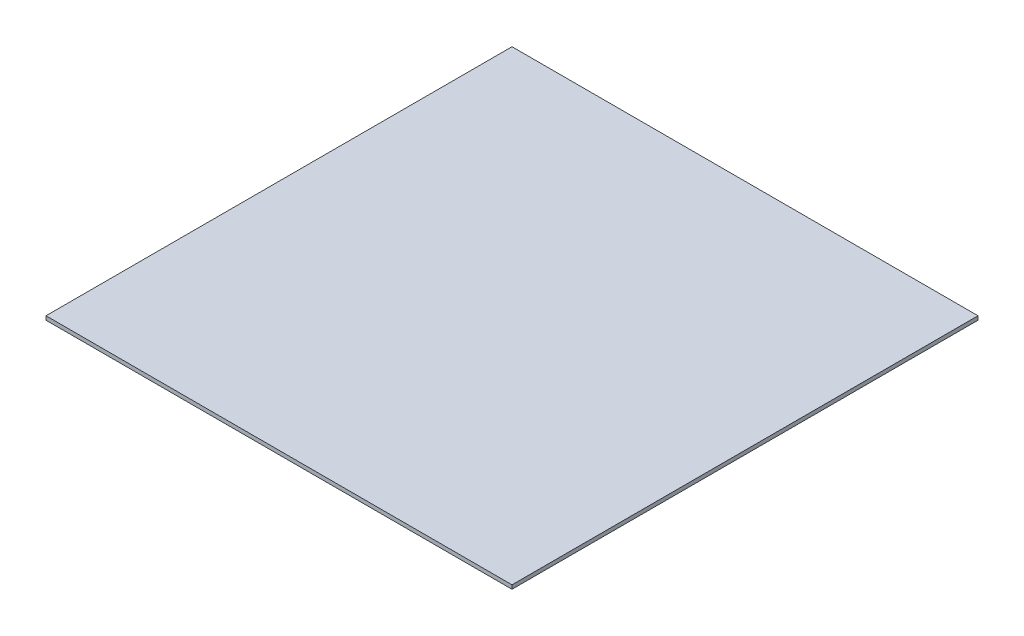
SolidWorks part; units mm, degrees
ref_plane "Front Plane" through (0, 0, 0) normal (0, 0, 1) x (1, 0, 0)
ref_plane "Top Plane" through (0, 0, 0) normal (0, 1, 0) x (1, 0, 0)
ref_plane "Right Plane" through (0, 0, 0) normal (1, 0, 0) x (0, 0, -1)
sketch "Sketch1" plane through (-19.0745, -1092.5733, -406.9173) normal (0, -1, 0) x (1, 0, 0)
  line L5 (-240, -240) -> (240, -240) construction
  line L6 (-240, -240) -> (-240, 240) construction
  line L7 (-240, 240) -> (240, 240) construction
  line L8 (240, -240) -> (240, 240) construction
  line L9 (-240, -240) -> (240, 240) construction
  line L10 (-240, 240) -> (240, -240) construction
  line L11 (300, -300) -> (-300, -300)
  line L12 (300, -300) -> (300, 300)
  line L13 (300, 300) -> (-300, 300)
  line L14 (-300, -300) -> (-300, 300)
  line L15 (300, -300) -> (-300, 300) construction
  line L16 (300, 300) -> (-300, -300) construction
  point P0 (0, 0)
  point P5 (0, 0)
  point P7 (-240, -240)
  dimension "D1" = 480
  dimension "D2" = 480
  dimension "D3" = 600
  dimension "D4" = 600
extrude "Boss-Extrude1" add sketch "Sketch1" along normal blind 5 contours L13 L14 L11 L12
sketch "Sketch3" plane through (0, -1092.5733, 0) normal (0, 1, 0) x (1, 0, 0)
  line L0 (-199.0745, 166.9173) -> (-199.0745, 226.9173)
  line L1 (-259.0745, 166.9173) -> (-199.0745, 166.9173)
  line L2 (-259.0745, 166.9173) -> (-259.0745, 226.9173)
  line L3 (-259.0745, 226.9173) -> (-199.0745, 226.9173)
  line L4 (-199.0745, 166.9173) -> (-199.0745, 226.9173)
  line L5 (-199.0745, 166.9173) -> (-139.0745, 166.9173)
  line L6 (-139.0745, 166.9173) -> (-139.0745, 226.9173)
  line L7 (-199.0745, 226.9173) -> (-139.0745, 226.9173)
  line L8 (-139.0745, 166.9173) -> (-139.0745, 226.9173)
  line L9 (-139.0745, 166.9173) -> (-79.0745, 166.9173)
  line L10 (-79.0745, 166.9173) -> (-79.0745, 226.9173)
  line L11 (-139.0745, 226.9173) -> (-79.0745, 226.9173)
  line L12 (-79.0745, 166.9173) -> (-79.0745, 226.9173)
  line L13 (-79.0745, 166.9173) -> (-19.0745, 166.9173)
  line L14 (-19.0745, 166.9173) -> (-19.0745, 226.9173)
  line L15 (-79.0745, 226.9173) -> (-19.0745, 226.9173)
  line L16 (-19.0745, 166.9173) -> (-19.0745, 226.9173)
  line L17 (-19.0745, 166.9173) -> (40.9255, 166.9173)
  line L18 (40.9255, 166.9173) -> (40.9255, 226.9173)
  line L19 (-19.0745, 226.9173) -> (40.9255, 226.9173)
  line L20 (40.9255, 166.9173) -> (40.9255, 226.9173)
  line L21 (40.9255, 166.9173) -> (100.9255, 166.9173)
  line L22 (100.9255, 166.9173) -> (100.9255, 226.9173)
  line L23 (40.9255, 226.9173) -> (100.9255, 226.9173)
  line L24 (100.9255, 166.9173) -> (100.9255, 226.9173)
  line L25 (100.9255, 166.9173) -> (160.9255, 166.9173)
  line L26 (160.9255, 166.9173) -> (160.9255, 226.9173)
  line L27 (100.9255, 226.9173) -> (160.9255, 226.9173)
  line L28 (160.9255, 166.9173) -> (160.9255, 226.9173)
  line L29 (160.9255, 166.9173) -> (220.9255, 166.9173)
  line L30 (220.9255, 166.9173) -> (220.9255, 226.9173)
  line L31 (160.9255, 226.9173) -> (220.9255, 226.9173)
  line L32 (-199.0745, 226.9173) -> (-199.0745, 286.9173)
  line L33 (-199.0745, 226.9173) -> (-139.0745, 226.9173)
  line L34 (-139.0745, 226.9173) -> (-139.0745, 286.9173)
  line L35 (-199.0745, 286.9173) -> (-139.0745, 286.9173)
  line L36 (-139.0745, 226.9173) -> (-139.0745, 286.9173)
  line L37 (-139.0745, 226.9173) -> (-79.0745, 226.9173)
  line L38 (-79.0745, 226.9173) -> (-79.0745, 286.9173)
  line L39 (-139.0745, 286.9173) -> (-79.0745, 286.9173)
  line L40 (-79.0745, 226.9173) -> (-79.0745, 286.9173)
  line L41 (-79.0745, 226.9173) -> (-19.0745, 226.9173)
  line L42 (-19.0745, 226.9173) -> (-19.0745, 286.9173)
  line L43 (-79.0745, 286.9173) -> (-19.0745, 286.9173)
  line L44 (-19.0745, 226.9173) -> (-19.0745, 286.9173)
  line L45 (-19.0745, 226.9173) -> (40.9255, 226.9173)
  line L46 (40.9255, 226.9173) -> (40.9255, 286.9173)
  line L47 (-19.0745, 286.9173) -> (40.9255, 286.9173)
  line L48 (40.9255, 226.9173) -> (40.9255, 286.9173)
  line L49 (40.9255, 226.9173) -> (100.9255, 226.9173)
  line L50 (100.9255, 226.9173) -> (100.9255, 286.9173)
  line L51 (40.9255, 286.9173) -> (100.9255, 286.9173)
  line L52 (100.9255, 226.9173) -> (100.9255, 286.9173)
  line L53 (100.9255, 226.9173) -> (160.9255, 226.9173)
  line L54 (160.9255, 226.9173) -> (160.9255, 286.9173)
  line L55 (100.9255, 286.9173) -> (160.9255, 286.9173)
  line L56 (160.9255, 226.9173) -> (160.9255, 286.9173)
  line L57 (160.9255, 226.9173) -> (220.9255, 226.9173)
  line L58 (220.9255, 226.9173) -> (220.9255, 286.9173)
  line L59 (160.9255, 286.9173) -> (220.9255, 286.9173)
  line L60 (-199.0745, 286.9173) -> (-199.0745, 346.9173)
  line L61 (-199.0745, 286.9173) -> (-139.0745, 286.9173)
  line L62 (-139.0745, 286.9173) -> (-139.0745, 346.9173)
  line L63 (-199.0745, 346.9173) -> (-139.0745, 346.9173)
  line L64 (-139.0745, 286.9173) -> (-139.0745, 346.9173)
  line L65 (-139.0745, 286.9173) -> (-79.0745, 286.9173)
  line L66 (-79.0745, 286.9173) -> (-79.0745, 346.9173)
  line L67 (-139.0745, 346.9173) -> (-79.0745, 346.9173)
  line L68 (-79.0745, 286.9173) -> (-79.0745, 346.9173)
  line L69 (-79.0745, 286.9173) -> (-19.0745, 286.9173)
  line L70 (-19.0745, 286.9173) -> (-19.0745, 346.9173)
  line L71 (-79.0745, 346.9173) -> (-19.0745, 346.9173)
  line L72 (-19.0745, 286.9173) -> (-19.0745, 346.9173)
  line L73 (-19.0745, 286.9173) -> (40.9255, 286.9173)
  line L74 (40.9255, 286.9173) -> (40.9255, 346.9173)
  line L75 (-19.0745, 346.9173) -> (40.9255, 346.9173)
  line L76 (40.9255, 286.9173) -> (40.9255, 346.9173)
  line L77 (40.9255, 286.9173) -> (100.9255, 286.9173)
  line L78 (100.9255, 286.9173) -> (100.9255, 346.9173)
  line L79 (40.9255, 346.9173) -> (100.9255, 346.9173)
  line L80 (100.9255, 286.9173) -> (100.9255, 346.9173)
  line L81 (100.9255, 286.9173) -> (160.9255, 286.9173)
  line L82 (160.9255, 286.9173) -> (160.9255, 346.9173)
  line L83 (100.9255, 346.9173) -> (160.9255, 346.9173)
  line L84 (160.9255, 286.9173) -> (160.9255, 346.9173)
  line L85 (160.9255, 286.9173) -> (220.9255, 286.9173)
  line L86 (220.9255, 286.9173) -> (220.9255, 346.9173)
  line L87 (160.9255, 346.9173) -> (220.9255, 346.9173)
  line L88 (-199.0745, 346.9173) -> (-199.0745, 406.9173)
  line L89 (-199.0745, 346.9173) -> (-139.0745, 346.9173)
  line L90 (-139.0745, 346.9173) -> (-139.0745, 406.9173)
  line L91 (-199.0745, 406.9173) -> (-139.0745, 406.9173)
  line L92 (-139.0745, 346.9173) -> (-139.0745, 406.9173)
  line L93 (-139.0745, 346.9173) -> (-79.0745, 346.9173)
  line L94 (-79.0745, 346.9173) -> (-79.0745, 406.9173)
  line L95 (-139.0745, 406.9173) -> (-79.0745, 406.9173)
  line L96 (-79.0745, 346.9173) -> (-79.0745, 406.9173)
  line L97 (-79.0745, 346.9173) -> (-19.0745, 346.9173)
  line L98 (-19.0745, 346.9173) -> (-19.0745, 406.9173)
  line L99 (-79.0745, 406.9173) -> (-19.0745, 406.9173)
  line L100 (-19.0745, 346.9173) -> (-19.0745, 406.9173)
  line L101 (-19.0745, 346.9173) -> (40.9255, 346.9173)
  line L102 (40.9255, 346.9173) -> (40.9255, 406.9173)
  line L103 (-19.0745, 406.9173) -> (40.9255, 406.9173)
  line L104 (40.9255, 346.9173) -> (40.9255, 406.9173)
  line L105 (40.9255, 346.9173) -> (100.9255, 346.9173)
  line L106 (100.9255, 346.9173) -> (100.9255, 406.9173)
  line L107 (40.9255, 406.9173) -> (100.9255, 406.9173)
  line L108 (100.9255, 346.9173) -> (100.9255, 406.9173)
  line L109 (100.9255, 346.9173) -> (160.9255, 346.9173)
  line L110 (160.9255, 346.9173) -> (160.9255, 406.9173)
  line L111 (100.9255, 406.9173) -> (160.9255, 406.9173)
  line L112 (160.9255, 346.9173) -> (160.9255, 406.9173)
  line L113 (160.9255, 346.9173) -> (220.9255, 346.9173)
  line L114 (220.9255, 346.9173) -> (220.9255, 406.9173)
  line L115 (160.9255, 406.9173) -> (220.9255, 406.9173)
  line L116 (-199.0745, 406.9173) -> (-199.0745, 466.9173)
  line L117 (-199.0745, 406.9173) -> (-139.0745, 406.9173)
  line L118 (-139.0745, 406.9173) -> (-139.0745, 466.9173)
  line L119 (-199.0745, 466.9173) -> (-139.0745, 466.9173)
  line L120 (-139.0745, 406.9173) -> (-139.0745, 466.9173)
  line L121 (-139.0745, 406.9173) -> (-79.0745, 406.9173)
  line L122 (-79.0745, 406.9173) -> (-79.0745, 466.9173)
  line L123 (-139.0745, 466.9173) -> (-79.0745, 466.9173)
  line L124 (-79.0745, 406.9173) -> (-79.0745, 466.9173)
  line L125 (-79.0745, 406.9173) -> (-19.0745, 406.9173)
  line L126 (-19.0745, 406.9173) -> (-19.0745, 466.9173)
  line L127 (-79.0745, 466.9173) -> (-19.0745, 466.9173)
  line L128 (-19.0745, 406.9173) -> (-19.0745, 466.9173)
  line L129 (-19.0745, 406.9173) -> (40.9255, 406.9173)
  line L130 (40.9255, 406.9173) -> (40.9255, 466.9173)
  line L131 (-19.0745, 466.9173) -> (40.9255, 466.9173)
  line L132 (40.9255, 406.9173) -> (40.9255, 466.9173)
  line L133 (40.9255, 406.9173) -> (100.9255, 406.9173)
  line L134 (100.9255, 406.9173) -> (100.9255, 466.9173)
  line L135 (40.9255, 466.9173) -> (100.9255, 466.9173)
  line L136 (100.9255, 406.9173) -> (100.9255, 466.9173)
  line L137 (100.9255, 406.9173) -> (160.9255, 406.9173)
  line L138 (160.9255, 406.9173) -> (160.9255, 466.9173)
  line L139 (100.9255, 466.9173) -> (160.9255, 466.9173)
  line L140 (160.9255, 406.9173) -> (160.9255, 466.9173)
  line L141 (160.9255, 406.9173) -> (220.9255, 406.9173)
  line L142 (220.9255, 406.9173) -> (220.9255, 466.9173)
  line L143 (160.9255, 466.9173) -> (220.9255, 466.9173)
  line L144 (-199.0745, 466.9173) -> (-199.0745, 526.9173)
  line L145 (-199.0745, 466.9173) -> (-139.0745, 466.9173)
  line L146 (-139.0745, 466.9173) -> (-139.0745, 526.9173)
  line L147 (-199.0745, 526.9173) -> (-139.0745, 526.9173)
  line L148 (-139.0745, 466.9173) -> (-139.0745, 526.9173)
  line L149 (-139.0745, 466.9173) -> (-79.0745, 466.9173)
  line L150 (-79.0745, 466.9173) -> (-79.0745, 526.9173)
  line L151 (-139.0745, 526.9173) -> (-79.0745, 526.9173)
  line L152 (-79.0745, 466.9173) -> (-79.0745, 526.9173)
  line L153 (-79.0745, 466.9173) -> (-19.0745, 466.9173)
  line L154 (-19.0745, 466.9173) -> (-19.0745, 526.9173)
  line L155 (-79.0745, 526.9173) -> (-19.0745, 526.9173)
  line L156 (-19.0745, 466.9173) -> (-19.0745, 526.9173)
  line L157 (-19.0745, 466.9173) -> (40.9255, 466.9173)
  line L158 (40.9255, 466.9173) -> (40.9255, 526.9173)
  line L159 (-19.0745, 526.9173) -> (40.9255, 526.9173)
  line L160 (40.9255, 466.9173) -> (40.9255, 526.9173)
  line L161 (40.9255, 466.9173) -> (100.9255, 466.9173)
  line L162 (100.9255, 466.9173) -> (100.9255, 526.9173)
  line L163 (40.9255, 526.9173) -> (100.9255, 526.9173)
  line L164 (100.9255, 466.9173) -> (100.9255, 526.9173)
  line L165 (100.9255, 466.9173) -> (160.9255, 466.9173)
  line L166 (160.9255, 466.9173) -> (160.9255, 526.9173)
  line L167 (100.9255, 526.9173) -> (160.9255, 526.9173)
  line L168 (160.9255, 466.9173) -> (160.9255, 526.9173)
  line L169 (160.9255, 466.9173) -> (220.9255, 466.9173)
  line L170 (220.9255, 466.9173) -> (220.9255, 526.9173)
  line L171 (160.9255, 526.9173) -> (220.9255, 526.9173)
  line L172 (-199.0745, 526.9173) -> (-199.0745, 586.9173)
  line L173 (-199.0745, 526.9173) -> (-139.0745, 526.9173)
  line L174 (-139.0745, 526.9173) -> (-139.0745, 586.9173)
  line L175 (-199.0745, 586.9173) -> (-139.0745, 586.9173)
  line L176 (-139.0745, 526.9173) -> (-139.0745, 586.9173)
  line L177 (-139.0745, 526.9173) -> (-79.0745, 526.9173)
  line L178 (-79.0745, 526.9173) -> (-79.0745, 586.9173)
  line L179 (-139.0745, 586.9173) -> (-79.0745, 586.9173)
  line L180 (-79.0745, 526.9173) -> (-79.0745, 586.9173)
  line L181 (-79.0745, 526.9173) -> (-19.0745, 526.9173)
  line L182 (-19.0745, 526.9173) -> (-19.0745, 586.9173)
  line L183 (-79.0745, 586.9173) -> (-19.0745, 586.9173)
  line L184 (-19.0745, 526.9173) -> (-19.0745, 586.9173)
  line L185 (-19.0745, 526.9173) -> (40.9255, 526.9173)
  line L186 (40.9255, 526.9173) -> (40.9255, 586.9173)
  line L187 (-19.0745, 586.9173) -> (40.9255, 586.9173)
  line L188 (40.9255, 526.9173) -> (40.9255, 586.9173)
  line L189 (40.9255, 526.9173) -> (100.9255, 526.9173)
  line L190 (100.9255, 526.9173) -> (100.9255, 586.9173)
  line L191 (40.9255, 586.9173) -> (100.9255, 586.9173)
  line L192 (100.9255, 526.9173) -> (100.9255, 586.9173)
  line L193 (100.9255, 526.9173) -> (160.9255, 526.9173)
  line L194 (160.9255, 526.9173) -> (160.9255, 586.9173)
  line L195 (100.9255, 586.9173) -> (160.9255, 586.9173)
  line L196 (160.9255, 526.9173) -> (160.9255, 586.9173)
  line L197 (160.9255, 526.9173) -> (220.9255, 526.9173)
  line L198 (220.9255, 526.9173) -> (220.9255, 586.9173)
  line L199 (160.9255, 586.9173) -> (220.9255, 586.9173)
  line L200 (-199.0745, 586.9173) -> (-199.0745, 646.9173)
  line L201 (-199.0745, 586.9173) -> (-139.0745, 586.9173)
  line L202 (-139.0745, 586.9173) -> (-139.0745, 646.9173)
  line L203 (-199.0745, 646.9173) -> (-139.0745, 646.9173)
  line L204 (-139.0745, 586.9173) -> (-139.0745, 646.9173)
  line L205 (-139.0745, 586.9173) -> (-79.0745, 586.9173)
  line L206 (-79.0745, 586.9173) -> (-79.0745, 646.9173)
  line L207 (-139.0745, 646.9173) -> (-79.0745, 646.9173)
  line L208 (-79.0745, 586.9173) -> (-79.0745, 646.9173)
  line L209 (-79.0745, 586.9173) -> (-19.0745, 586.9173)
  line L210 (-19.0745, 586.9173) -> (-19.0745, 646.9173)
  line L211 (-79.0745, 646.9173) -> (-19.0745, 646.9173)
  line L212 (-19.0745, 586.9173) -> (-19.0745, 646.9173)
  line L213 (-19.0745, 586.9173) -> (40.9255, 586.9173)
  line L214 (40.9255, 586.9173) -> (40.9255, 646.9173)
  line L215 (-19.0745, 646.9173) -> (40.9255, 646.9173)
  line L216 (40.9255, 586.9173) -> (40.9255, 646.9173)
  line L217 (40.9255, 586.9173) -> (100.9255, 586.9173)
  line L218 (100.9255, 586.9173) -> (100.9255, 646.9173)
  line L219 (40.9255, 646.9173) -> (100.9255, 646.9173)
  line L220 (100.9255, 586.9173) -> (100.9255, 646.9173)
  line L221 (100.9255, 586.9173) -> (160.9255, 586.9173)
  line L222 (160.9255, 586.9173) -> (160.9255, 646.9173)
  line L223 (100.9255, 646.9173) -> (160.9255, 646.9173)
  line L224 (160.9255, 586.9173) -> (160.9255, 646.9173)
  line L225 (160.9255, 586.9173) -> (220.9255, 586.9173)
  line L226 (220.9255, 586.9173) -> (220.9255, 646.9173)
  line L227 (160.9255, 646.9173) -> (220.9255, 646.9173)
  line L228 (-259.0745, 226.9173) -> (-259.0745, 286.9173)
  line L229 (-259.0745, 226.9173) -> (-199.0745, 226.9173)
  line L230 (-199.0745, 226.9173) -> (-199.0745, 286.9173)
  line L231 (-259.0745, 286.9173) -> (-199.0745, 286.9173)
  line L232 (-259.0745, 286.9173) -> (-259.0745, 346.9173)
  line L233 (-259.0745, 286.9173) -> (-199.0745, 286.9173)
  line L234 (-199.0745, 286.9173) -> (-199.0745, 346.9173)
  line L235 (-259.0745, 346.9173) -> (-199.0745, 346.9173)
  line L236 (-259.0745, 346.9173) -> (-259.0745, 406.9173)
  line L237 (-259.0745, 346.9173) -> (-199.0745, 346.9173)
  line L238 (-199.0745, 346.9173) -> (-199.0745, 406.9173)
  line L239 (-259.0745, 406.9173) -> (-199.0745, 406.9173)
  line L240 (-259.0745, 406.9173) -> (-259.0745, 466.9173)
  line L241 (-259.0745, 406.9173) -> (-199.0745, 406.9173)
  line L242 (-199.0745, 406.9173) -> (-199.0745, 466.9173)
  line L243 (-259.0745, 466.9173) -> (-199.0745, 466.9173)
  line L244 (-259.0745, 466.9173) -> (-259.0745, 526.9173)
  line L245 (-259.0745, 466.9173) -> (-199.0745, 466.9173)
  line L246 (-199.0745, 466.9173) -> (-199.0745, 526.9173)
  line L247 (-259.0745, 526.9173) -> (-199.0745, 526.9173)
  line L248 (-259.0745, 526.9173) -> (-259.0745, 586.9173)
  line L249 (-259.0745, 526.9173) -> (-199.0745, 526.9173)
  line L250 (-199.0745, 526.9173) -> (-199.0745, 586.9173)
  line L251 (-259.0745, 586.9173) -> (-199.0745, 586.9173)
  line L252 (-259.0745, 586.9173) -> (-259.0745, 646.9173)
  line L253 (-259.0745, 586.9173) -> (-199.0745, 586.9173)
  line L254 (-199.0745, 586.9173) -> (-199.0745, 646.9173)
  line L255 (-259.0745, 646.9173) -> (-199.0745, 646.9173)
  line L256 (-259.0745, 196.9173) -> (-229.0745, 196.9173) construction
  line L257 (-229.0745, 196.9173) -> (-229.0745, 166.9173) construction
  line L258 (-229.0745, 196.9173) -> (-169.0745, 196.9173) construction
  circle A0 centre (-229.0745, 196.9173) radius 10 construction
  circle A1 centre (-229.0745, 196.9173) radius 12.5 construction
  circle A2 centre (-169.0745, 196.9173) radius 12.5 construction
  circle A4 centre (-199.0745, 196.9173) radius 17.5 construction
  dimension "D5" = 35
  dimension "D1" = 60
  dimension "D2" = 60
  dimension "D3" = 8
  dimension "D4" = 8
